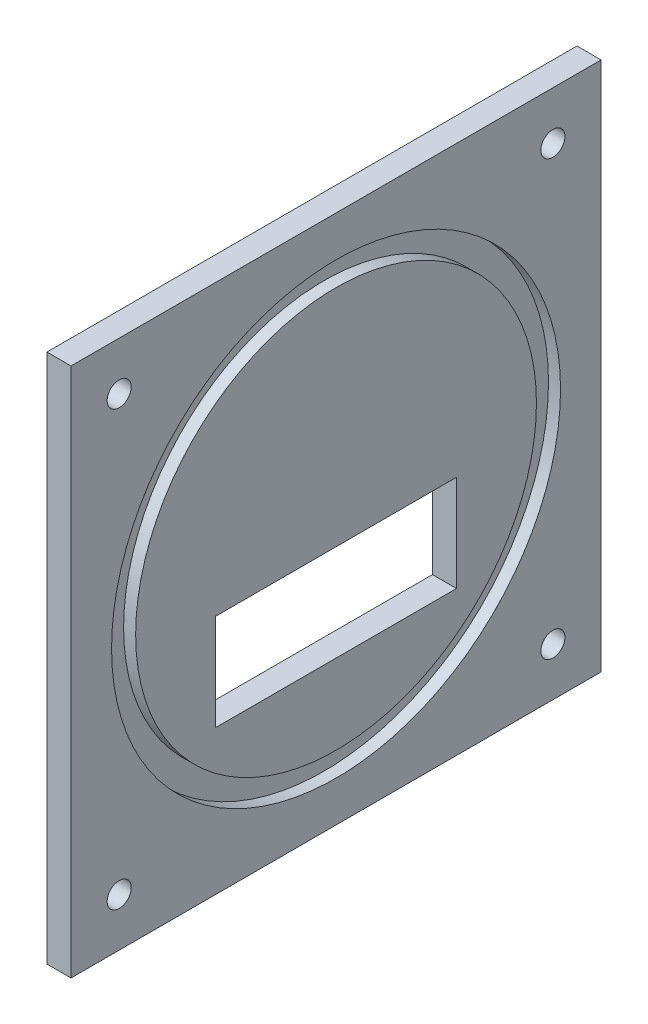
SolidWorks part; units mm, degrees
ref_plane "Front Plane" through (0, 0, 0) normal (0, 0, 1) x (1, 0, 0)
ref_plane "Top Plane" through (0, 0, 0) normal (0, 1, 0) x (1, 0, 0)
ref_plane "Right Plane" through (0, 0, 0) normal (1, 0, 0) x (0, 0, -1)
sketch "Sketch1" plane through (0, 0, 0) normal (1, 0, 0) x (0, 0, -1)
  line L1 (0, 0) -> (220, 0)
  line L2 (0, 0) -> (0, 220)
  line L3 (0, 220) -> (220, 220)
  line L4 (220, 0) -> (220, 220)
  line L5 (60, 100) -> (160, 100)
  line L6 (60, 100) -> (60, 60)
  line L7 (60, 60) -> (160, 60)
  line L8 (160, 100) -> (160, 60)
  dimension "D1" = 220
  dimension "D2" = 220
  dimension "D3" = 40
  dimension "D4" = 100
  dimension "D5" = 60
  dimension "D6" = 60
extrude "Boss-Extrude1" add sketch "Sketch1" along normal blind 10
sketch "Sketch2" plane through (10, 0, 0) normal (1, 0, 0) x (0, 0, -1)
  circle A0 centre (110, 110) radius 93.1728
  circle A1 centre (110, 110) radius 83.1728
  dimension "D1" = 186.3457
  dimension "D2" = 10
extrude "Cut-Extrude1" cut sketch "Sketch2" against normal blind 5
sketch "Sketch3" plane through (10, 0, 0) normal (1, 0, 0) x (0, 0, -1)
  line L0 (220, 220) -> (0, 220) construction
  line L1 (0, 220) -> (0, 0) construction
  line L2 (0, 0) -> (220, 0) construction
  line L3 (220, 0) -> (220, 220) construction
  circle A0 centre (20, 200) radius 5
  circle A1 centre (200, 200) radius 5
  circle A2 centre (200, 20) radius 5
  circle A3 centre (20, 20) radius 5
  dimension "D1" = 10
  dimension "D2" = 20
  dimension "D3" = 20
  dimension "D4" = 20
  dimension "D5" = 20
extrude "Cut-Extrude2" cut sketch "Sketch3" against normal through all
